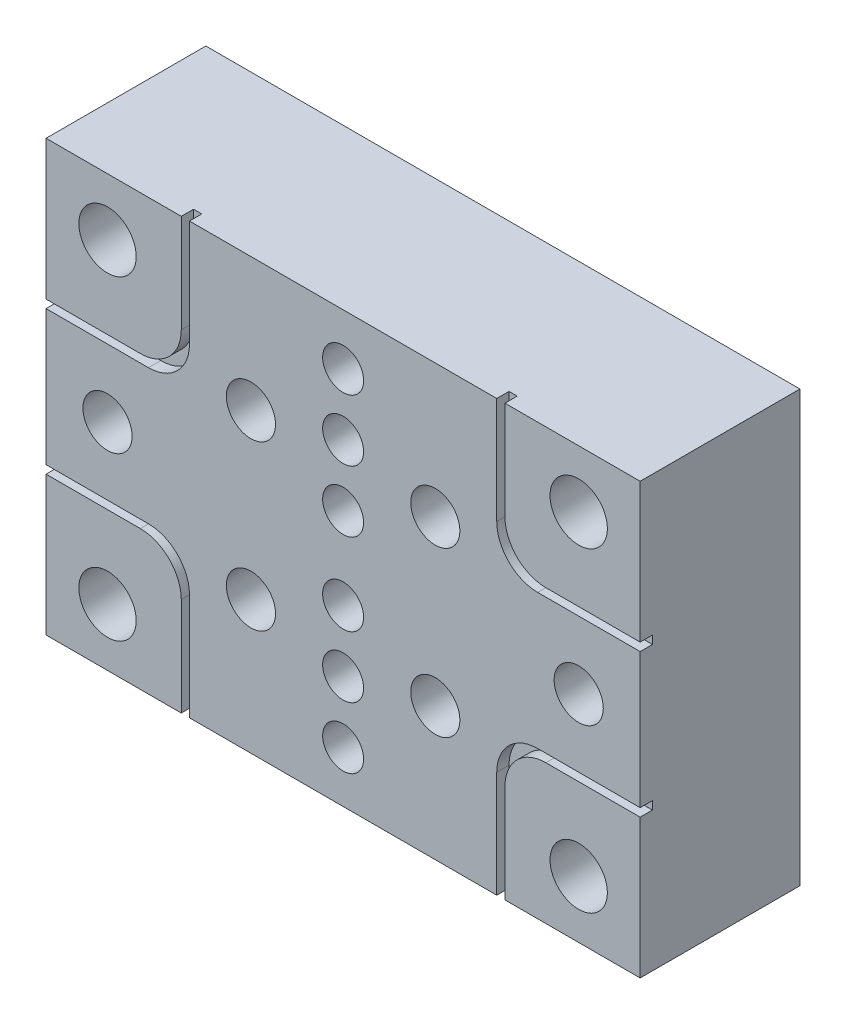
SolidWorks part; units mm, degrees
ref_plane "Alzado" through (0, 0, 0) normal (0, 0, 1) x (1, 0, 0)
ref_plane "Planta" through (0, 0, 0) normal (0, 1, 0) x (1, 0, 0)
ref_plane "Vista lateral" through (0, 0, 0) normal (1, 0, 0) x (0, 0, -1)
sketch "Croquis1" plane through (0, 0, 0) normal (0, 0, 1) x (1, 0, 0)
  line L1 (-72.5, -52.5) -> (72.5, -52.5)
  line L2 (-72.5, -52.5) -> (-72.5, 52.5)
  line L3 (-72.5, 52.5) -> (72.5, 52.5)
  line L4 (72.5, -52.5) -> (72.5, 52.5)
  dimension "D1" = 145
  dimension "D2" = 105
  dimension "D3" = 52.5
  dimension "D4" = 72.5
extrude "Saliente-Extruir1" add sketch "Croquis1" along normal blind 39
hole_wizard "Taladro1" positions "Croquis4" profile "Croquis5" legacy end condition through all
sketch "Croquis4" plane through (0, 0, 39) normal (0, 0, 1) x (1, 0, 0)
  line L0 (72.5, 52.5) -> (-72.5, 52.5) construction
  line L1 (-72.5, 52.5) -> (-72.5, -52.5) construction
  point P0 (-57.5, 38.5)
  dimension "D1" = 14
  dimension "D2" = 15
sketch "Croquis5" plane through (-57.5, 38.5, 39) normal (1, 0, 0) x (0, -1, 0)
  line L0 (0, 0) -> (0, 39)
  line L1 (0, 39) -> (7, 39)
  line L2 (7, 39) -> (7, 0)
  line L3 (7, 0) -> (0, 0)
  line L4 (0, 110) -> (0, -10) construction
  dimension "Diámetro" = 14
  dimension "Profundidad" = 39
mirror "Simetría1" about plane through (0, 0, 0) normal (0, 1, 0) of "Taladro1"
mirror "Simetría2" about plane through (0, 0, 0) normal (1, 0, 0) of "Simetría1", "Taladro1"
hole_wizard "Taladro de margen para M1.61" positions "Croquis6" profile "Croquis7" hole size "M1.6" standard "Ansi Metric"
sketch "Croquis6" plane through (0, 0, 39) normal (0, 0, 1) x (1, 0, 0)
  point P0 (0, 40)
  point P2 (0, 25)
  point P4 (0, 10)
  dimension "D1" = 40
  dimension "D2" = 25
  dimension "D3" = 10
sketch "Croquis7" plane through (0, 40, 39) normal (1, 0, 0) x (0, -1, 0)
  line L0 (0, 0) -> (0, 28.0043)
  line L1 (0, 28.0043) -> (5, 25)
  line L2 (5, 25) -> (5, 0)
  line L5 (5, 0) -> (0, 0)
  line L10 (0, 28.0043) -> (-5, 25) construction
  line L11 (0, -6.35) -> (0, 107.95) construction
  dimension "Diámetro de taladro" = 10
  dimension "Profundidad de taladro" = 25
  dimension "Ángulo de perforador" = 118
mirror "Simetría3" about plane through (0, 0, 0) normal (0, 1, 0) of "Taladro de margen para M1.61"
hole_wizard "Taladro de margen para M1.62" positions "Croquis8" profile "Croquis9" hole size "M1.6" standard "Ansi Metric"
sketch "Croquis8" plane through (0, 0, 39) normal (0, 0, 1) x (1, 0, 0)
  line L0 (-72.5, 52.5) -> (-72.5, -52.5) construction
  point P0 (-57.5, 0)
  point P2 (-22.5, 20)
  point P4 (-22.5, -20)
  dimension "D1" = 15
  dimension "D2" = 50
  dimension "D3" = 50
  dimension "D4" = 20
  dimension "D5" = 20
sketch "Croquis9" plane through (-57.5, 0, 39) normal (1, 0, 0) x (0, -1, 0)
  line L0 (0, 0) -> (0, 21.6052)
  line L1 (0, 21.6052) -> (6, 18)
  line L2 (6, 18) -> (6, 0)
  line L5 (6, 0) -> (0, 0)
  line L10 (0, 21.6052) -> (-6, 18) construction
  line L11 (0, -6.35) -> (0, 107.95) construction
  dimension "Diámetro de taladro" = 12
  dimension "Profundidad de taladro" = 18
  dimension "Ángulo de perforador" = 118
mirror "Simetría4" about plane through (0, 0, 0) normal (1, 0, 0) of "Taladro de margen para M1.62"
sketch "Croquis10" plane through (0, 0, 39) normal (0, 0, 1) x (1, 0, 0)
  line L0 (-37.5, 52.5) -> (-37.5, 26.5)
  line L1 (72.5, 52.5) -> (-72.5, 52.5) construction
  line L2 (-47.5, 16.5) -> (-72.5, 16.5)
  line L3 (-72.5, 52.5) -> (-72.5, -52.5) construction
  line L4 (-39.5, 52.5) -> (-39.5, 28.5)
  line L5 (-49.5, 18.5) -> (-72.5, 18.5)
  line L6 (-37.5, 52.5) -> (-39.5, 52.5)
  line L7 (-72.5, 18.5) -> (-72.5, 16.5)
  line L8 (-39.5, 52.5) -> (-39.5, 18.5) construction
  line L9 (-39.5, 18.5) -> (-72.5, 18.5) construction
  line L10 (-37.5, 52.5) -> (-37.5, 16.5) construction
  line L11 (-37.5, 16.5) -> (-72.5, 16.5) construction
  arc A0 (-39.5, 28.5) -> (-49.5, 18.5) centre (-49.5, 28.5) cw
  arc A1 (-37.5, 26.5) -> (-47.5, 16.5) centre (-47.5, 26.5) cw
  dimension "D4" = 10
  dimension "D1" = 35
  dimension "D2" = 36
  dimension "D3" = 2
extrude "Cortar-Extruir1" cut sketch "Croquis10" against normal blind 3
mirror "Simetría5" about plane through (0, 0, 0) normal (0, 1, 0) of "Cortar-Extruir1"
mirror "Simetría6" about plane through (0, 0, 0) normal (1, 0, 0) of "Simetría5", "Cortar-Extruir1"
